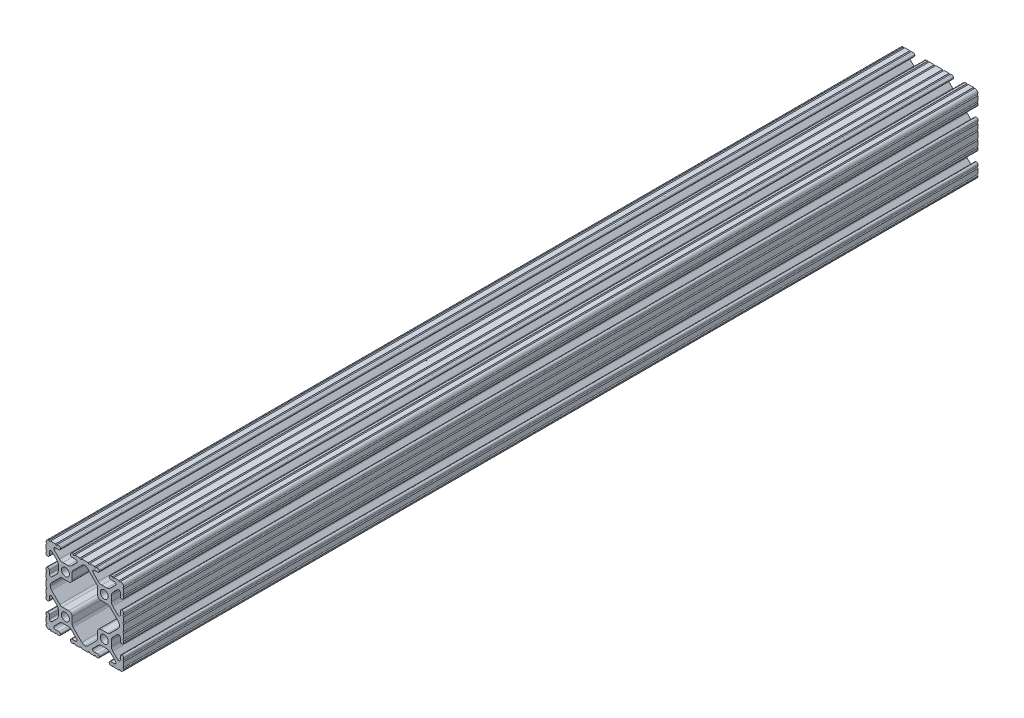
SolidWorks part; units mm, degrees
ref_plane "Front Plane" through (0, 0, 0) normal (0, 0, 1) x (1, 0, 0)
ref_plane "Top Plane" through (0, 0, 0) normal (0, 1, 0) x (1, 0, 0)
ref_plane "Right Plane" through (0, 0, 0) normal (1, 0, 0) x (0, 0, -1)
ref_plane "Plane1" through (0, 0, -3683) normal (0, 0, -1) x (-1, 0, 0)
sketch "Sketch1" plane through (0, 0, -3683) normal (0, 0, -1) x (-1, 0, 0)
  line L0 (-4.2026, -12.7) -> (-3.729, -12.7)
  line L1 (-3.2268, -12.7) -> (-1.6073, -12.7)
  line L2 (-1.1051, -12.7) -> (1.1051, -12.7)
  line L3 (1.6073, -12.7) -> (3.2268, -12.7)
  line L4 (3.729, -12.7) -> (4.2026, -12.7)
  line L5 (4.7308, -12.1794) -> (4.7308, -12.1157)
  line L6 (4.2026, -11.5951) -> (3.0439, -11.5951)
  line L7 (2.694, -10.7504) -> (4.3815, -9.0629)
  line L8 (5.504, -8.5979) -> (7.196, -8.5979)
  line L9 (8.3185, -9.0629) -> (10.006, -10.7504)
  line L10 (9.6488, -11.595) -> (8.4899, -11.595)
  line L11 (7.9693, -12.1157) -> (7.9693, -12.1792)
  line L12 (8.4974, -12.7) -> (9.067, -12.7)
  line L13 (9.5692, -12.7) -> (11.2066, -12.7)
  line L14 (11.7088, -12.7) -> (11.725, -12.7)
  line L15 (12.7, -11.647) -> (12.7, -11.6343)
  line L16 (12.7, -11.1263) -> (12.7, -9.5126)
  line L17 (12.7, -9.0046) -> (12.7, -8.458)
  line L18 (12.1793, -7.9373) -> (12.1158, -7.9373)
  line L19 (11.5951, -8.458) -> (11.5951, -9.5505)
  line L20 (10.7279, -9.9097) -> (9.1391, -8.3209)
  line L21 (8.6741, -7.1984) -> (8.6741, -5.5017)
  line L22 (9.1404, -4.3779) -> (10.7283, -2.7938)
  line L23 (11.5951, -3.1534) -> (11.5951, -4.242)
  line L24 (12.1158, -4.7627) -> (12.1793, -4.7627)
  line L25 (12.7, -4.242) -> (12.7, -3.6638)
  line L26 (12.7, -3.1558) -> (12.7, -1.5421)
  line L27 (12.7, -1.0341) -> (12.7, 1.0341)
  line L28 (12.7, 1.5421) -> (12.7, 3.1558)
  line L29 (12.7, 3.6638) -> (12.7, 4.242)
  line L30 (12.1793, 4.7627) -> (12.1158, 4.7627)
  line L31 (11.5951, 4.242) -> (11.5951, 3.1534)
  line L32 (10.7283, 2.7938) -> (9.1404, 4.3779)
  line L33 (8.6741, 5.5017) -> (8.6741, 7.1984)
  line L34 (9.1391, 8.3209) -> (10.7279, 9.9097)
  line L35 (11.5951, 9.5505) -> (11.5951, 8.458)
  line L36 (12.1158, 7.9373) -> (12.1793, 7.9373)
  line L37 (12.7, 8.458) -> (12.7, 9.0046)
  line L38 (12.7, 9.5126) -> (12.7, 11.1263)
  line L39 (12.7, 11.6343) -> (12.7, 11.647)
  line L40 (11.725, 12.7) -> (11.7088, 12.7)
  line L41 (11.2066, 12.7) -> (9.5692, 12.7)
  line L42 (9.067, 12.7) -> (8.4974, 12.7)
  line L43 (7.9693, 12.1792) -> (7.9693, 12.1157)
  line L44 (8.49, 11.595) -> (9.6488, 11.595)
  line L45 (10.006, 10.7504) -> (8.3185, 9.0629)
  line L46 (7.196, 8.5979) -> (5.504, 8.5979)
  line L47 (4.3815, 9.0629) -> (2.694, 10.7504)
  line L48 (3.0439, 11.5951) -> (4.2026, 11.5951)
  line L49 (4.7308, 12.1157) -> (4.7308, 12.1794)
  line L50 (4.2026, 12.7) -> (3.729, 12.7)
  line L51 (3.2268, 12.7) -> (1.6073, 12.7)
  line L52 (1.1051, 12.7) -> (-1.1051, 12.7)
  line L53 (-1.6073, 12.7) -> (-3.2268, 12.7)
  line L54 (-3.729, 12.7) -> (-4.2026, 12.7)
  line L55 (-4.7308, 12.1794) -> (-4.7308, 12.1157)
  line L56 (-4.2026, 11.5951) -> (-3.0439, 11.5951)
  line L57 (-2.694, 10.7504) -> (-4.3815, 9.0629)
  line L58 (-5.504, 8.5979) -> (-7.196, 8.5979)
  line L59 (-8.3185, 9.0629) -> (-10.006, 10.7504)
  line L60 (-9.6488, 11.595) -> (-8.49, 11.595)
  line L61 (-7.9693, 12.1157) -> (-7.9693, 12.1792)
  line L62 (-8.4974, 12.7) -> (-9.067, 12.7)
  line L63 (-9.5692, 12.7) -> (-11.2066, 12.7)
  line L64 (-11.7088, 12.7) -> (-11.725, 12.7)
  line L65 (-12.7, 11.647) -> (-12.7, 11.6343)
  line L66 (-12.7, 11.1263) -> (-12.7, 9.5126)
  line L67 (-12.7, 9.0046) -> (-12.7, 8.458)
  line L68 (-12.1793, 7.9373) -> (-12.1158, 7.9373)
  line L69 (-11.5951, 8.458) -> (-11.5951, 9.5505)
  line L70 (-10.7279, 9.9097) -> (-9.1391, 8.3209)
  line L71 (-8.6741, 7.1984) -> (-8.6741, 5.5017)
  line L72 (-9.1404, 4.3779) -> (-10.7283, 2.7938)
  line L73 (-11.5951, 3.1534) -> (-11.5951, 4.242)
  line L74 (-12.1158, 4.7627) -> (-12.1793, 4.7627)
  line L75 (-12.7, 4.242) -> (-12.7, 3.6638)
  line L76 (-12.7, 3.1558) -> (-12.7, 1.5421)
  line L77 (-12.7, 1.0341) -> (-12.7, -1.0341)
  line L78 (-12.7, -1.5421) -> (-12.7, -3.1558)
  line L79 (-12.7, -3.6638) -> (-12.7, -4.242)
  line L80 (-12.1793, -4.7627) -> (-12.1158, -4.7627)
  line L81 (-11.5951, -4.242) -> (-11.5951, -3.1534)
  line L82 (-10.7283, -2.7938) -> (-9.1404, -4.3779)
  line L83 (-8.6741, -5.5017) -> (-8.6741, -7.1984)
  line L84 (-9.1391, -8.3209) -> (-10.7279, -9.9097)
  line L85 (-11.5951, -9.5505) -> (-11.5951, -8.458)
  line L86 (-12.1158, -7.9373) -> (-12.1793, -7.9373)
  line L87 (-12.7, -8.458) -> (-12.7, -9.0046)
  line L88 (-12.7, -9.5126) -> (-12.7, -11.1263)
  line L89 (-12.7, -11.6343) -> (-12.7, -11.647)
  line L90 (-11.725, -12.7) -> (-11.7088, -12.7)
  line L91 (-11.2066, -12.7) -> (-9.5692, -12.7)
  line L92 (-9.067, -12.7) -> (-8.4974, -12.7)
  line L93 (-7.9693, -12.1792) -> (-7.9693, -12.1157)
  line L94 (-8.49, -11.595) -> (-9.6488, -11.595)
  line L95 (-10.006, -10.7504) -> (-8.3185, -9.0629)
  line L96 (-7.196, -8.5979) -> (-5.504, -8.5979)
  line L97 (-4.3815, -9.0629) -> (-2.694, -10.7504)
  line L98 (-3.0439, -11.5951) -> (-4.2026, -11.5951)
  line L99 (-4.7308, -12.1157) -> (-4.7308, -12.1794)
  line L100 (3.842, -8.0398) -> (0.9939, -10.8879)
  line L101 (-0.9939, -10.8879) -> (-3.842, -8.0398)
  line L102 (-4.1656, -7.2586) -> (-4.1656, -5.1943)
  line L103 (-5.2705, -4.0894) -> (-7.4082, -4.0894)
  line L104 (-8.1886, -3.7667) -> (-10.8867, -1.0751)
  line L105 (-11.3157, -0.0411) -> (-11.3157, 0.0411)
  line L106 (-10.8867, 1.0751) -> (-8.1884, 3.7669)
  line L107 (-7.408, 4.0896) -> (-5.2705, 4.0896)
  line L108 (-4.1656, 5.1945) -> (-4.1656, 7.2586)
  line L109 (-3.842, 8.0398) -> (-0.8978, 10.984)
  line L110 (0.8978, 10.984) -> (3.842, 8.0398)
  line L111 (4.1656, 7.2586) -> (4.1656, 5.1943)
  line L112 (5.2705, 4.0894) -> (7.4082, 4.0894)
  line L113 (8.1886, 3.7667) -> (10.8867, 1.0751)
  line L114 (11.3157, 0.0411) -> (11.3157, -0.0411)
  line L115 (10.8867, -1.0751) -> (8.1886, -3.7667)
  line L116 (7.4082, -4.0894) -> (5.2705, -4.0894)
  line L117 (4.1656, -5.1943) -> (4.1656, -7.2586)
  arc A0 (-3.729, -12.7) -> (-3.2268, -12.7) centre (-3.4779, -12.6617) cw
  arc A1 (-1.6073, -12.7) -> (-1.1051, -12.7) centre (-1.3562, -12.6617) cw
  arc A2 (1.1051, -12.7) -> (1.6073, -12.7) centre (1.3562, -12.6617) cw
  arc A3 (3.2268, -12.7) -> (3.729, -12.7) centre (3.4779, -12.6617) cw
  arc A4 (4.2026, -12.7) -> (4.7308, -12.1794) centre (4.2101, -12.1794) ccw
  arc A5 (4.7308, -12.1157) -> (4.2026, -11.5951) centre (4.2101, -12.1157) ccw
  arc A6 (3.0439, -11.5951) -> (2.694, -10.7504) centre (3.0439, -11.1003) cw
  arc A7 (4.3815, -9.0629) -> (5.504, -8.5979) centre (5.504, -10.1854) cw
  arc A8 (7.196, -8.5979) -> (8.3185, -9.0629) centre (7.196, -10.1854) cw
  arc A9 (10.006, -10.7504) -> (9.6488, -11.595) centre (9.6561, -11.1003) cw
  arc A10 (8.4899, -11.595) -> (7.9693, -12.1157) centre (8.4899, -12.1157) ccw
  arc A11 (7.9693, -12.1792) -> (8.4974, -12.7) centre (8.4899, -12.1794) ccw
  arc A12 (9.067, -12.7) -> (9.5692, -12.7) centre (9.3181, -12.6617) cw
  arc A13 (11.2066, -12.7) -> (11.7088, -12.7) centre (11.4577, -12.6617) cw
  arc A14 (11.725, -12.7) -> (12.7, -11.647) centre (11.6459, -11.6489) ccw
  arc A15 (12.7, -11.6343) -> (12.7, -11.1263) centre (12.7, -11.3803) cw
  arc A16 (12.7, -9.5126) -> (12.7, -9.0046) centre (12.7, -9.2586) cw
  arc A17 (12.7, -8.458) -> (12.1793, -7.9373) centre (12.1793, -8.458) ccw
  arc A18 (12.1158, -7.9373) -> (11.5951, -8.458) centre (12.1158, -8.458) ccw
  arc A19 (11.5951, -9.5505) -> (10.7279, -9.9097) centre (11.0871, -9.5505) cw
  arc A20 (9.1391, -8.3209) -> (8.6741, -7.1984) centre (10.2616, -7.1984) cw
  arc A21 (8.6741, -5.5017) -> (9.1404, -4.3779) centre (10.2616, -5.5017) cw
  arc A22 (10.7283, -2.7938) -> (11.5951, -3.1534) centre (11.0871, -3.1534) cw
  arc A23 (11.5951, -4.242) -> (12.1158, -4.7627) centre (12.1158, -4.242) ccw
  arc A24 (12.1793, -4.7627) -> (12.7, -4.242) centre (12.1793, -4.242) ccw
  arc A25 (12.7, -3.6638) -> (12.7, -3.1558) centre (12.7, -3.4098) cw
  arc A26 (12.7, -1.5421) -> (12.7, -1.0341) centre (12.7, -1.2881) cw
  arc A27 (12.7, 1.0341) -> (12.7, 1.5421) centre (12.7, 1.2881) cw
  arc A28 (12.7, 3.1558) -> (12.7, 3.6638) centre (12.7, 3.4098) cw
  arc A29 (12.7, 4.242) -> (12.1793, 4.7627) centre (12.1793, 4.242) ccw
  arc A30 (12.1158, 4.7627) -> (11.5951, 4.242) centre (12.1158, 4.242) ccw
  arc A31 (11.5951, 3.1534) -> (10.7283, 2.7938) centre (11.0871, 3.1534) cw
  arc A32 (9.1404, 4.3779) -> (8.6741, 5.5017) centre (10.2616, 5.5017) cw
  arc A33 (8.6741, 7.1984) -> (9.1391, 8.3209) centre (10.2616, 7.1984) cw
  arc A34 (10.7279, 9.9097) -> (11.5951, 9.5505) centre (11.0871, 9.5505) cw
  arc A35 (11.5951, 8.458) -> (12.1158, 7.9373) centre (12.1158, 8.458) ccw
  arc A36 (12.1793, 7.9373) -> (12.7, 8.458) centre (12.1793, 8.458) ccw
  arc A37 (12.7, 9.0046) -> (12.7, 9.5126) centre (12.7, 9.2586) cw
  arc A38 (12.7, 11.1263) -> (12.7, 11.6343) centre (12.7, 11.3803) cw
  arc A39 (12.7, 11.647) -> (11.725, 12.7) centre (11.6459, 11.6489) ccw
  arc A40 (11.7088, 12.7) -> (11.2066, 12.7) centre (11.4577, 12.6617) cw
  arc A41 (9.5692, 12.7) -> (9.067, 12.7) centre (9.3181, 12.6617) cw
  arc A42 (8.4974, 12.7) -> (7.9693, 12.1792) centre (8.4899, 12.1794) ccw
  arc A43 (7.9693, 12.1157) -> (8.49, 11.595) centre (8.49, 12.1157) ccw
  arc A44 (9.6488, 11.595) -> (10.006, 10.7504) centre (9.6561, 11.1003) cw
  arc A45 (8.3185, 9.0629) -> (7.196, 8.5979) centre (7.196, 10.1854) cw
  arc A46 (5.504, 8.5979) -> (4.3815, 9.0629) centre (5.504, 10.1854) cw
  arc A47 (2.694, 10.7504) -> (3.0439, 11.5951) centre (3.0439, 11.1003) cw
  arc A48 (4.2026, 11.5951) -> (4.7308, 12.1157) centre (4.2101, 12.1157) ccw
  arc A49 (4.7308, 12.1794) -> (4.2026, 12.7) centre (4.2101, 12.1794) ccw
  arc A50 (3.729, 12.7) -> (3.2268, 12.7) centre (3.4779, 12.6617) cw
  arc A51 (1.6073, 12.7) -> (1.1051, 12.7) centre (1.3562, 12.6617) cw
  arc A52 (-1.1051, 12.7) -> (-1.6073, 12.7) centre (-1.3562, 12.6617) cw
  arc A53 (-3.2268, 12.7) -> (-3.729, 12.7) centre (-3.4779, 12.6617) cw
  arc A54 (-4.2026, 12.7) -> (-4.7308, 12.1794) centre (-4.2101, 12.1794) ccw
  arc A55 (-4.7308, 12.1157) -> (-4.2026, 11.5951) centre (-4.2101, 12.1157) ccw
  arc A56 (-3.0439, 11.5951) -> (-2.694, 10.7504) centre (-3.0439, 11.1003) cw
  arc A57 (-4.3815, 9.0629) -> (-5.504, 8.5979) centre (-5.504, 10.1854) cw
  arc A58 (-7.196, 8.5979) -> (-8.3185, 9.0629) centre (-7.196, 10.1854) cw
  arc A59 (-10.006, 10.7504) -> (-9.6488, 11.595) centre (-9.6561, 11.1003) cw
  arc A60 (-8.49, 11.595) -> (-7.9693, 12.1157) centre (-8.49, 12.1157) ccw
  arc A61 (-7.9693, 12.1792) -> (-8.4974, 12.7) centre (-8.4899, 12.1794) ccw
  arc A62 (-9.067, 12.7) -> (-9.5692, 12.7) centre (-9.3181, 12.6617) cw
  arc A63 (-11.2066, 12.7) -> (-11.7088, 12.7) centre (-11.4577, 12.6617) cw
  arc A64 (-11.725, 12.7) -> (-12.7, 11.647) centre (-11.6459, 11.6489) ccw
  arc A65 (-12.7, 11.6343) -> (-12.7, 11.1263) centre (-12.7, 11.3803) cw
  arc A66 (-12.7, 9.5126) -> (-12.7, 9.0046) centre (-12.7, 9.2586) cw
  arc A67 (-12.7, 8.458) -> (-12.1793, 7.9373) centre (-12.1793, 8.458) ccw
  arc A68 (-12.1158, 7.9373) -> (-11.5951, 8.458) centre (-12.1158, 8.458) ccw
  arc A69 (-11.5951, 9.5505) -> (-10.7279, 9.9097) centre (-11.0871, 9.5505) cw
  arc A70 (-9.1391, 8.3209) -> (-8.6741, 7.1984) centre (-10.2616, 7.1984) cw
  arc A71 (-8.6741, 5.5017) -> (-9.1404, 4.3779) centre (-10.2616, 5.5017) cw
  arc A72 (-10.7283, 2.7938) -> (-11.5951, 3.1534) centre (-11.0871, 3.1534) cw
  arc A73 (-11.5951, 4.242) -> (-12.1158, 4.7627) centre (-12.1158, 4.242) ccw
  arc A74 (-12.1793, 4.7627) -> (-12.7, 4.242) centre (-12.1793, 4.242) ccw
  arc A75 (-12.7, 3.6638) -> (-12.7, 3.1558) centre (-12.7, 3.4098) cw
  arc A76 (-12.7, 1.5421) -> (-12.7, 1.0341) centre (-12.7, 1.2881) cw
  arc A77 (-12.7, -1.0341) -> (-12.7, -1.5421) centre (-12.7, -1.2881) cw
  arc A78 (-12.7, -3.1558) -> (-12.7, -3.6638) centre (-12.7, -3.4098) cw
  arc A79 (-12.7, -4.242) -> (-12.1793, -4.7627) centre (-12.1793, -4.242) ccw
  arc A80 (-12.1158, -4.7627) -> (-11.5951, -4.242) centre (-12.1158, -4.242) ccw
  arc A81 (-11.5951, -3.1534) -> (-10.7283, -2.7938) centre (-11.0871, -3.1534) cw
  arc A82 (-9.1404, -4.3779) -> (-8.6741, -5.5017) centre (-10.2616, -5.5017) cw
  arc A83 (-8.6741, -7.1984) -> (-9.1391, -8.3209) centre (-10.2616, -7.1984) cw
  arc A84 (-10.7279, -9.9097) -> (-11.5951, -9.5505) centre (-11.0871, -9.5505) cw
  arc A85 (-11.5951, -8.458) -> (-12.1158, -7.9373) centre (-12.1158, -8.458) ccw
  arc A86 (-12.1793, -7.9373) -> (-12.7, -8.458) centre (-12.1793, -8.458) ccw
  arc A87 (-12.7, -9.0046) -> (-12.7, -9.5126) centre (-12.7, -9.2586) cw
  arc A88 (-12.7, -11.1263) -> (-12.7, -11.6343) centre (-12.7, -11.3803) cw
  arc A89 (-12.7, -11.647) -> (-11.725, -12.7) centre (-11.6459, -11.6489) ccw
  arc A90 (-11.7088, -12.7) -> (-11.2066, -12.7) centre (-11.4577, -12.6617) cw
  arc A91 (-9.5692, -12.7) -> (-9.067, -12.7) centre (-9.3181, -12.6617) cw
  arc A92 (-8.4974, -12.7) -> (-7.9693, -12.1792) centre (-8.4899, -12.1794) ccw
  arc A93 (-7.9693, -12.1157) -> (-8.49, -11.595) centre (-8.49, -12.1157) ccw
  arc A94 (-9.6488, -11.595) -> (-10.006, -10.7504) centre (-9.6561, -11.1003) cw
  arc A95 (-8.3185, -9.0629) -> (-7.196, -8.5979) centre (-7.196, -10.1854) cw
  arc A96 (-5.504, -8.5979) -> (-4.3815, -9.0629) centre (-5.504, -10.1854) cw
  arc A97 (-2.694, -10.7504) -> (-3.0439, -11.5951) centre (-3.0439, -11.1003) cw
  arc A98 (-4.2026, -11.5951) -> (-4.7308, -12.1157) centre (-4.2101, -12.1157) ccw
  arc A99 (-4.7308, -12.1794) -> (-4.2026, -12.7) centre (-4.2101, -12.1794) ccw
  circle A100 centre (-6.35, -6.35) radius 1.3017
  arc A101 (4.1656, -7.2586) -> (3.842, -8.0398) centre (3.0607, -7.2586) cw
  arc A102 (0.9939, -10.8879) -> (0, -11.3152) centre (-0.0388, -9.8552) cw
  arc A103 (0, -11.3152) -> (-0.9939, -10.8879) centre (0.0388, -9.8552) cw
  arc A104 (-3.842, -8.0398) -> (-4.1656, -7.2586) centre (-3.0607, -7.2586) cw
  arc A105 (-4.1656, -5.1943) -> (-5.2705, -4.0894) centre (-5.2705, -5.1943) ccw
  arc A106 (-7.4082, -4.0894) -> (-8.1886, -3.7667) centre (-7.4082, -2.9845) cw
  arc A107 (-10.8867, -1.0751) -> (-11.3157, -0.0411) centre (-9.8552, -0.0411) cw
  arc A108 (-11.3157, 0.0411) -> (-10.8867, 1.0751) centre (-9.8552, 0.0411) cw
  arc A109 (-8.1884, 3.7669) -> (-7.408, 4.0896) centre (-7.408, 2.9847) cw
  arc A110 (-5.2705, 4.0896) -> (-4.1656, 5.1945) centre (-5.2705, 5.1945) ccw
  arc A111 (-4.1656, 7.2586) -> (-3.842, 8.0398) centre (-3.0607, 7.2586) cw
  arc A112 (-0.8978, 10.984) -> (0, 11.4056) centre (0.135, 9.9513) cw
  arc A113 (0, 11.4056) -> (0.8978, 10.984) centre (-0.135, 9.9513) cw
  arc A114 (3.842, 8.0398) -> (4.1656, 7.2586) centre (3.0607, 7.2586) cw
  arc A115 (4.1656, 5.1943) -> (5.2705, 4.0894) centre (5.2705, 5.1943) ccw
  arc A116 (7.4082, 4.0894) -> (8.1886, 3.7667) centre (7.4082, 2.9845) cw
  arc A117 (10.8867, 1.0751) -> (11.3157, 0.0411) centre (9.8552, 0.0411) cw
  arc A118 (11.3157, -0.0411) -> (10.8867, -1.0751) centre (9.8552, -0.0411) cw
  arc A119 (8.1886, -3.7667) -> (7.4082, -4.0894) centre (7.4082, -2.9845) cw
  arc A120 (5.2705, -4.0894) -> (4.1656, -5.1943) centre (5.2705, -5.1943) ccw
  circle A121 centre (6.35, -6.35) radius 1.3017
  circle A122 centre (6.35, 6.35) radius 1.3017
  circle A123 centre (-6.35, 6.35) radius 1.3017
  dimension "D1" = 25.4
  dimension "D2" = 25.4
extrude "Boss-Extrude1" add sketch "Sketch1" against normal blind 279.4
